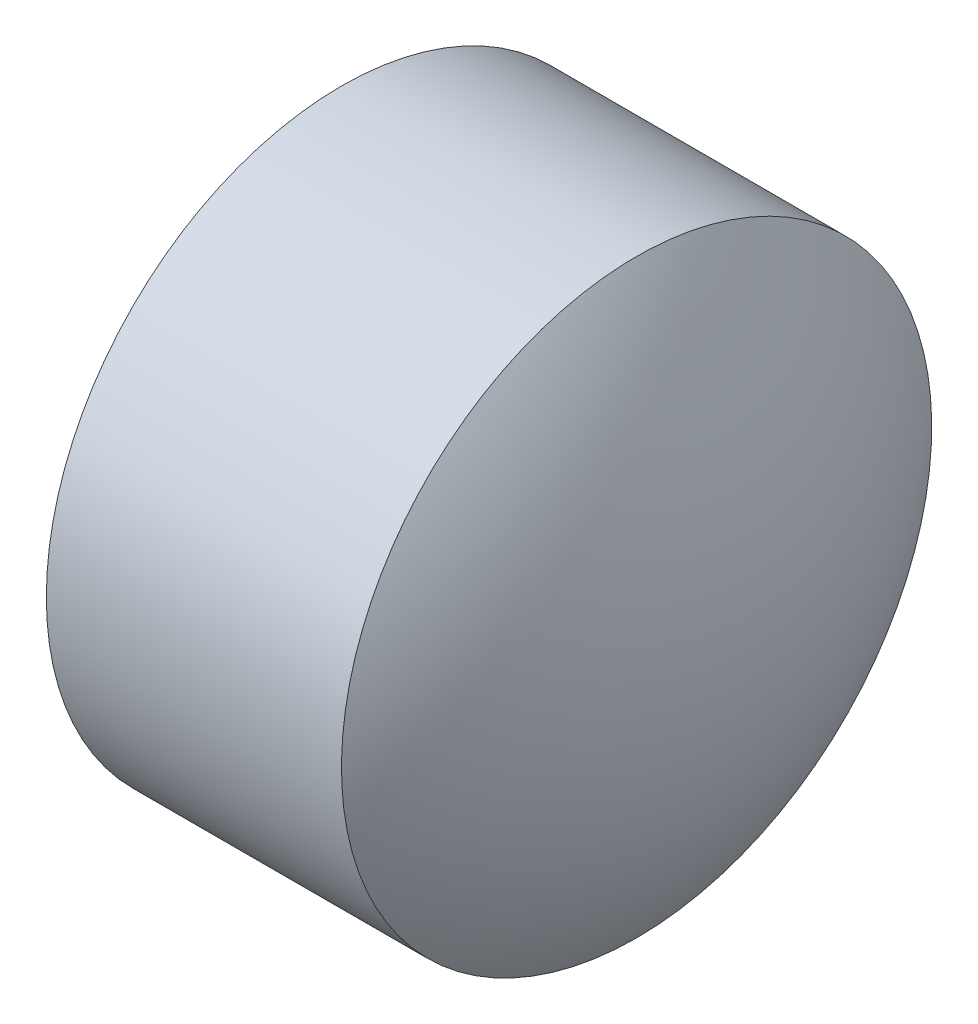
SolidWorks part; units mm, degrees
ref_plane "前视基准面" through (0, 0, 0) normal (0, 0, 1) x (1, 0, 0)
ref_plane "上视基准面" through (0, 0, 0) normal (0, 1, 0) x (1, 0, 0)
ref_plane "右视基准面" through (0, 0, 0) normal (1, 0, 0) x (0, 0, -1)
sketch "草图2" plane through (0, 0, 0) normal (0, 0, 1) x (1, 0, 0)
  line L0 (6.3077, 4.828) -> (7.3077, 4.828)
  line L1 (7.3077, 4.828) -> (7.3077, 2.828)
  line L2 (7.3077, 2.828) -> (6.3077, 2.828)
  line L3 (6.3077, 2.828) -> (6.3077, 4.828)
  line L4 (5.8779, 3.828) -> (7.7375, 3.828) construction
  arc A0 (6.3077, 4.828) -> (6.3077, 2.828) centre (7.7375, 3.828) ccw
  arc A1 (7.3077, 2.828) -> (7.3077, 4.828) centre (5.8779, 3.828) ccw
  dimension "D1" = 1
  dimension "D2" = 2
revolve "旋转1" add sketch "草图2" angle 360 about L4
